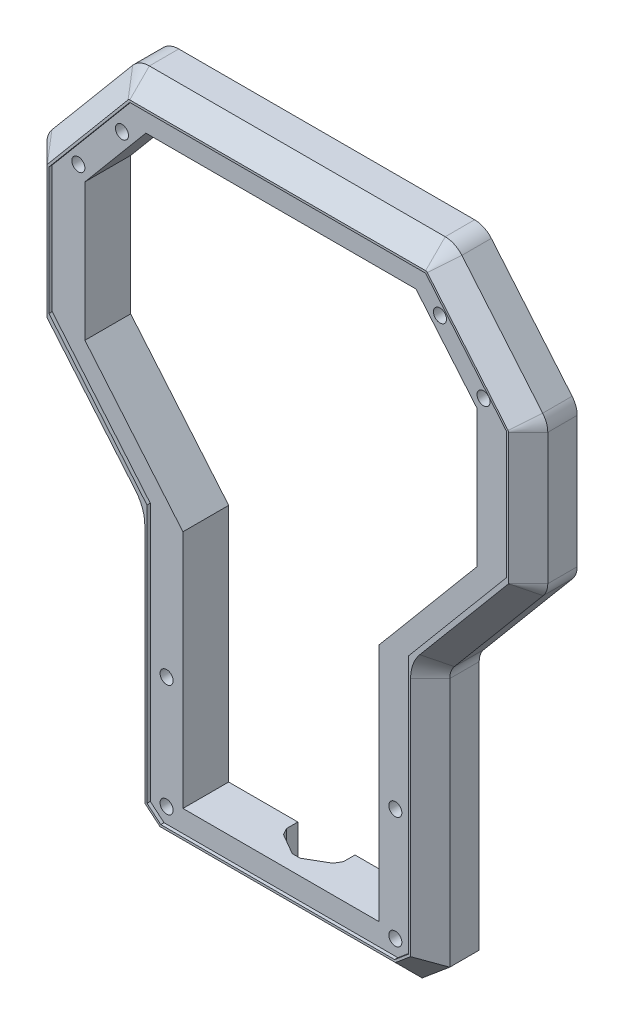
SolidWorks part; units mm, degrees
ref_plane "Plano frontal" through (0, 0, 0) normal (0, 0, 1) x (1, 0, 0)
ref_plane "Plano superior" through (0, 0, 0) normal (0, 1, 0) x (1, 0, 0)
ref_plane "Plano direito" through (0, 0, 0) normal (1, 0, 0) x (0, 0, -1)
sketch "Esboço1" plane through (0, 0, 0) normal (0, 0, 1) x (1, 0, 0)
  line L0 (-57.3196, -8.0822) -> (57.3196, -8.0822)
  line L1 (-70, 2.5579) -> (-70, 117.2967)
  line L2 (-72.1215, 123.1254) -> (-112.8785, 171.6978)
  line L3 (-115, 177.5265) -> (-115, 237.7125)
  line L4 (-67.9074, 291.9178) -> (67.9074, 291.9178)
  line L5 (0, 291.9178) -> (0, 0) construction
  line L6 (-75.5678, 288.3457) -> (-112.6604, 244.1404)
  line L7 (-90, 175.5467) -> (-90, 238.5381)
  line L8 (-90, 238.5381) -> (-61.9911, 271.9178)
  line L9 (45, 11.9178) -> (-45, 11.9178)
  line L10 (-45, 11.9178) -> (-45, 121.9178)
  line L11 (-45, 121.9178) -> (-90, 175.5467)
  line L12 (-70, 2.5579) -> (-57.3196, -8.0822)
  line L13 (70, 2.5579) -> (57.3196, -8.0822)
  line L14 (-61.9911, 271.9178) -> (61.9911, 271.9178)
  line L17 (45, 121.9178) -> (90, 175.5467)
  line L18 (45, 11.9178) -> (45, 121.9178)
  line L19 (90, 238.5381) -> (61.9911, 271.9178)
  line L20 (90, 175.5467) -> (90, 238.5381)
  line L21 (75.5678, 288.3457) -> (112.6604, 244.1404)
  line L22 (115, 177.5265) -> (115, 237.7125)
  line L23 (72.1215, 123.1254) -> (112.8785, 171.6978)
  line L24 (70, 2.5579) -> (70, 117.2967)
  arc A0 (-115, 237.7125) -> (-112.6604, 244.1404) centre (-105, 237.7125) cw
  arc A1 (-112.8785, 171.6978) -> (-115, 177.5265) centre (-105.9321, 177.5265) cw
  arc A2 (-70, 117.2967) -> (-72.1215, 123.1254) centre (-79.0679, 117.2967) ccw
  arc A3 (67.9074, 291.9178) -> (75.5678, 288.3457) centre (67.9074, 281.9178) cw
  arc A4 (-67.9074, 291.9178) -> (-75.5678, 288.3457) centre (-67.9074, 281.9178) ccw
  arc A5 (70, 117.2967) -> (72.1215, 123.1254) centre (79.0679, 117.2967) cw
  arc A6 (112.8785, 171.6978) -> (115, 177.5265) centre (105.9321, 177.5265) ccw
  arc A7 (115, 237.7125) -> (112.6604, 244.1404) centre (105, 237.7125) ccw
  point P27 (-115, 241.3522)
  point P33 (0, 11.9178)
  point P40 (0, 271.9178)
  point P46 (0, 11.9178)
  point P47 (115, 241.3522)
  point P53 (0, 280)
  dimension "D7" = 40
  dimension "D12" = 10
  dimension "D14" = 10
  dimension "D19" = 110
  dimension "D16" = 40
  dimension "D5" = 40
  dimension "D2" = 115
  dimension "D3" = 300
  dimension "D4" = 70
  dimension "D6" = 40
  dimension "D8" = 20
  dimension "D9" = 20
  dimension "D10" = 25
  dimension "D11" = 20
  dimension "D13" = 40
  dimension "D15" = 25
extrude "Ressalto-extrusão1" add sketch "Esboço1" along normal mid plane 45
chamfer "Chanfro1" distance 9 angle 45 20 edges at (0, -8.0822, 22.5) (-70, 59.9273, 22.5) (-70.5469, 120.3981, 22.5) (-92.5, 147.4116, 22.5) (0, 291.9178, 22.5) (-114.4531, 174.4251, 22.5) (-94.1141, 266.243, 22.5) (-115, 207.6195, 22.5) (70, 59.9273, 22.5) (70.5469, 120.3981, 22.5) (92.5, 147.4116, 22.5) (114.4531, 174.4251, 22.5) (115, 207.6195, 22.5) (114.3969, 241.1327, 22.5) (94.1141, 266.243, 22.5) (72.1336, 290.9809, 22.5) (-72.1336, 290.9809, 22.5) (-114.3969, 241.1327, 22.5) (-63.6598, -2.7621, 22.5) (63.6598, -2.7621, 22.5)
sketch "Esboço3" plane through (0, 0, 0) normal (0, 0, 1) x (1, 0, 0)
  line L1 (-722.7729, 507.4347) -> (416.458, 507.4347)
  line L2 (-722.7729, 507.4347) -> (-722.7729, -202.3634)
  line L3 (-722.7729, -202.3634) -> (416.458, -202.3634)
  line L4 (416.458, 507.4347) -> (416.458, -202.3634)
extrude "Corte-extrusão1" cut sketch "Esboço3" against normal up to next
sketch "Esboço4" plane through (0, 0, 22.5) normal (0, 0, 1) x (1, 0, 0)
  line L0 (-90, 175.5467) -> (-90, 238.5381)
  line L1 (-45, 121.9178) -> (-90, 175.5467)
  line L2 (-45, 121.9178) -> (-90, 175.5467) construction
  line L3 (-45, 11.9178) -> (-45, 121.9178)
  line L4 (-60, 7.221) -> (-53.6799, 1.9178)
  line L5 (0, -6.7811) -> (0, 343.2781) construction
  line L6 (-45, 11.9178) -> (45, 11.9178)
  line L7 (-61, 117.2967) -> (-61, 6.7547) construction
  line L8 (60, 7.221) -> (53.6799, 1.9178)
  line L9 (-53.6799, 1.9178) -> (53.6799, 1.9178)
  line L10 (90, 238.5381) -> (61.9911, 271.9178) construction
  line L11 (-90, 238.5381) -> (-61.9911, 271.9178)
  line L12 (-61.9911, 271.9178) -> (61.9911, 271.9178)
  line L13 (-105, 237.7125) -> (-67.9074, 281.9178)
  line L14 (-105, 237.7125) -> (-105, 179.4215)
  line L15 (-105, 179.4215) -> (-60, 125.7926)
  line L16 (-60, 125.7926) -> (-60, 7.221)
  line L17 (90, 175.5467) -> (90, 238.5381) construction
  line L18 (61.9911, 271.9178) -> (90, 238.5381)
  line L19 (-67.9074, 281.9178) -> (67.9074, 281.9178)
  line L20 (60, 125.7926) -> (60, 7.221)
  line L21 (105, 179.4215) -> (60, 125.7926)
  line L22 (105, 237.7125) -> (105, 179.4215)
  line L23 (-61, 6.7547) -> (-54.0438, 0.9178) construction
  line L24 (45, 11.9178) -> (45, 121.9178)
  line L25 (45, 121.9178) -> (90, 175.5467)
  line L26 (90, 238.5381) -> (90, 175.5467)
  line L27 (67.9074, 281.9178) -> (105, 237.7125)
  line L28 (-68.6734, 282.5606) -> (-105.766, 238.3553) construction
  line L29 (105.766, 238.3553) -> (68.6734, 282.5606) construction
  line L30 (-54.0438, 0.9178) -> (54.0438, 0.9178) construction
  line L31 (54.0438, 0.9178) -> (61, 6.7547) construction
  dimension "D1" = 15
  dimension "D2" = 10
  dimension "D3" = 9
  dimension "D4" = 15
  dimension "D5" = 1
  dimension "D6" = 10
  dimension "D7" = 1
  dimension "D8" = 1
  dimension "D9" = 1
  dimension "D10" = 15
  dimension "D11" = 1
extrude "Corte-extrusão5" cut sketch "Esboço4" against normal blind 1.5
sketch "Esboço5" plane through (0, 0, 21) normal (0, 0, 1) x (1, 0, 0)
  line L0 (-53.6799, 1.9178) -> (53.6799, 1.9178) construction
  line L1 (-105, 237.7125) -> (-105, 179.4215) construction
  line L2 (-60, 125.7926) -> (-60, 7.221) construction
  line L3 (0, -34.4878) -> (0, 335.3959) construction
  line L5 (-105, 237.7125) -> (-105, 179.4215) construction
  line L7 (67.9074, 281.9178) -> (-67.9074, 281.9178) construction
  line L8 (-60, 125.7926) -> (-60, 7.221) construction
  circle A0 centre (-93, 244) radius 3
  circle A1 centre (-52.5, 60.3962) radius 3
  circle A2 centre (-73, 266.9178) radius 3
  circle A3 centre (-52.5, 8.9178) radius 3
  circle A4 centre (52.5, 8.9178) radius 3
  circle A5 centre (73, 266.9178) radius 3
  circle A6 centre (52.5, 60.3962) radius 3
  circle A7 centre (93, 244) radius 3
  dimension "D1" = 15
  dimension "D3" = 7.5
  dimension "D4" = 7.5
  dimension "D5" = 32
  dimension "D6" = 7
  dimension "D2" = 12
extrude "Corte-extrusão6" cut sketch "Esboço5" against normal through all
sketch "Esboço7" plane through (0, 0, 0) normal (0, 0, -1) x (-1, 0, 0)
  line L1 (-73, 270.9592) -> (-76.5, 268.9385)
  line L2 (-76.5, 268.9385) -> (-76.5, 264.8971)
  line L3 (-76.5, 264.8971) -> (-73, 262.8763)
  line L4 (-73, 262.8763) -> (-69.5, 264.8971)
  line L5 (-69.5, 264.8971) -> (-69.5, 268.9385)
  line L6 (-69.5, 268.9385) -> (-73, 270.9592)
  line L7 (73, 270.9592) -> (69.5, 268.9385)
  line L8 (69.5, 268.9385) -> (69.5, 264.8971)
  line L9 (69.5, 264.8971) -> (73, 262.8763)
  line L10 (73, 262.8763) -> (76.5, 264.8971)
  line L11 (76.5, 264.8971) -> (76.5, 268.9385)
  line L12 (76.5, 268.9385) -> (73, 270.9592)
  line L13 (-93, 248.0415) -> (-96.5, 246.0207)
  line L14 (-96.5, 246.0207) -> (-96.5, 241.9793)
  line L15 (-96.5, 241.9793) -> (-93, 239.9585)
  line L16 (-93, 239.9585) -> (-89.5, 241.9793)
  line L17 (-89.5, 241.9793) -> (-89.5, 246.0207)
  line L18 (-89.5, 246.0207) -> (-93, 248.0415)
  line L19 (-52.5, 64.4377) -> (-56, 62.417)
  line L20 (-56, 62.417) -> (-56, 58.3755)
  line L21 (-56, 58.3755) -> (-52.5, 56.3548)
  line L22 (-52.5, 56.3548) -> (-49, 58.3755)
  line L23 (-49, 58.3755) -> (-49, 62.417)
  line L24 (-49, 62.417) -> (-52.5, 64.4377)
  line L25 (-52.5, 12.9592) -> (-56, 10.9385)
  line L26 (-56, 10.9385) -> (-56, 6.8971)
  line L27 (-56, 6.8971) -> (-52.5, 4.8763)
  line L28 (-52.5, 4.8763) -> (-49, 6.8971)
  line L29 (-49, 6.8971) -> (-49, 10.9385)
  line L30 (-49, 10.9385) -> (-52.5, 12.9592)
  line L31 (52.5, 12.9592) -> (49, 10.9385)
  line L32 (49, 10.9385) -> (49, 6.8971)
  line L33 (49, 6.8971) -> (52.5, 4.8763)
  line L34 (52.5, 4.8763) -> (56, 6.8971)
  line L35 (56, 6.8971) -> (56, 10.9385)
  line L36 (56, 10.9385) -> (52.5, 12.9592)
  line L37 (52.5, 64.4377) -> (49, 62.417)
  line L38 (49, 62.417) -> (49, 58.3755)
  line L39 (49, 58.3755) -> (52.5, 56.3548)
  line L40 (52.5, 56.3548) -> (56, 58.3755)
  line L41 (56, 58.3755) -> (56, 62.417)
  line L42 (56, 62.417) -> (52.5, 64.4377)
  line L43 (93, 248.0415) -> (89.5, 246.0207)
  line L44 (89.5, 246.0207) -> (89.5, 241.9793)
  line L45 (89.5, 241.9793) -> (93, 239.9585)
  line L46 (93, 239.9585) -> (96.5, 241.9793)
  line L47 (96.5, 241.9793) -> (96.5, 246.0207)
  line L48 (96.5, 246.0207) -> (93, 248.0415)
  circle A0 centre (-73, 266.9178) radius 3.5 construction
  circle A1 centre (73, 266.9178) radius 3.5 construction
  circle A2 centre (-93, 244) radius 3.5 construction
  circle A3 centre (-52.5, 60.3962) radius 3.5 construction
  circle A4 centre (-52.5, 8.9178) radius 3.5 construction
  circle A5 centre (52.5, 8.9178) radius 3.5 construction
  circle A6 centre (52.5, 60.3962) radius 3.5 construction
  circle A7 centre (93, 244) radius 3.5 construction
extrude "Corte-extrusão8" cut sketch "Esboço7" against normal blind 10
sketch "Esboço9" plane through (0, 0, 21) normal (0, 0, 1) x (1, 0, 0)
  line L0 (-105, 237.7125) -> (-90, 238.5381)
  line L1 (-90, 238.5381) -> (-90, 175.5467)
  line L2 (-90, 175.5467) -> (-45, 121.9178)
  line L3 (-45, 121.9178) -> (-60, 125.7926)
  line L4 (-60, 125.7926) -> (-105, 179.4215)
  line L5 (-105, 179.4215) -> (-105, 237.7125)
  line L6 (105, 237.7125) -> (90, 238.5381)
  line L7 (90, 238.5381) -> (90, 175.5467)
  line L8 (90, 175.5467) -> (45, 121.9178)
  line L9 (45, 121.9178) -> (60, 125.7926)
  line L10 (60, 125.7926) -> (105, 179.4215)
  line L11 (105, 179.4215) -> (105, 237.7125)
extrude "Corte-extrusão10" [suppressed] cut sketch "Esboço9" against normal up to next
sketch "Esboço12" plane through (0, 11.9178, 0) normal (0, 1, 0) x (1, 0, 0)
  line L0 (-1.9056, 14.341) -> (-11.4578, 8.826)
  line L1 (-11.4578, 8.826) -> (-13.2378, 5.743)
  line L2 (-13.2378, 5.743) -> (-13.2378, -5.287)
  line L3 (-13.2378, -5.287) -> (-11.4598, -8.3668)
  line L4 (-11.4598, -8.3668) -> (-1.9159, -13.8769)
  line L5 (-1.9159, -13.8769) -> (1.6402, -13.8769)
  line L6 (1.6402, -13.8769) -> (11.2209, -8.3455)
  line L7 (11.2209, -8.3455) -> (12.9867, -5.287)
  line L8 (12.9867, -5.287) -> (12.9867, 5.743)
  line L9 (12.9867, 5.743) -> (11.2067, 8.826)
  line L10 (11.2067, 8.826) -> (1.6544, 14.341)
  line L11 (1.6544, 14.341) -> (-1.9056, 14.341)
  dimension "D1" = 11.03
  dimension "D2" = 3.56
  dimension "D3" = 11.03
  dimension "D4" = 3.56
  dimension "D5" = 11.03
  dimension "D6" = 3.56
  dimension "D7" = 11.03
extrude "Corte-extrusão12" cut sketch "Esboço12" against normal blind 15
sketch "Esboço13" plane through (0, -8.0822, 0) normal (0, -1, 0) x (1, 0, 0)
  circle A0 centre (0, 0) radius 10.5
extrude "Corte-extrusão13" cut sketch "Esboço13" against normal blind 5
